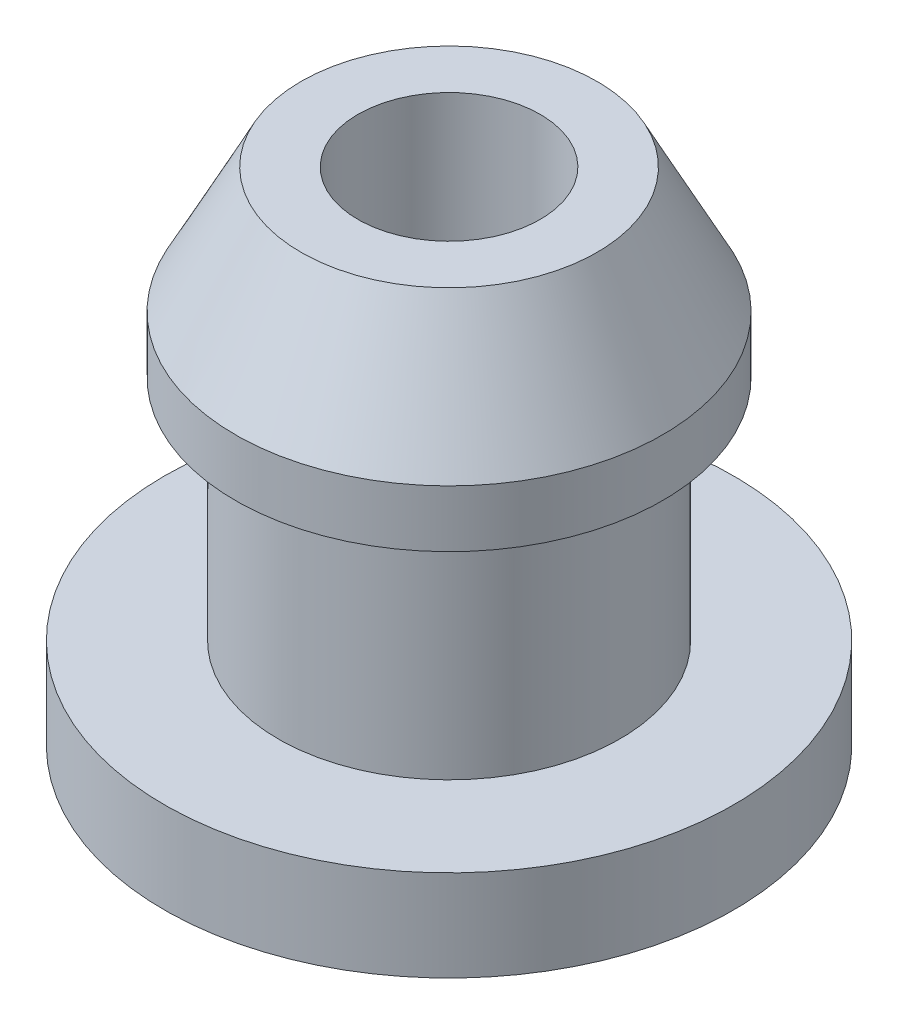
SolidWorks part; units mm, degrees
ref_plane "Plan de face" through (0, 0, 0) normal (0, 0, 1) x (1, 0, 0)
ref_plane "Plan de dessus" through (0, 0, 0) normal (0, 1, 0) x (1, 0, 0)
ref_plane "Plan de droite" through (0, 0, 0) normal (1, 0, 0) x (0, 0, -1)
sketch "Esquisse1" plane through (0, 0, 0) normal (0, 0, 1) x (1, 0, 0)
  line L0 (0, 5.28) -> (0, -4.4) construction
  line L1 (0, -4.4) -> (5, -4.4)
  line L2 (5, -4.4) -> (5, -2.8)
  line L3 (5, -2.8) -> (3, -2.8)
  line L4 (3, -2.8) -> (3, 1.2)
  line L5 (3, 1.2) -> (3.75, 1.2)
  line L6 (3.75, 1.2) -> (3.75, 2.2)
  line L7 (3.75, 2.2) -> (2.6, 4.4)
  line L8 (0, -1.6) -> (1.6, -1.6)
  line L9 (1.6, -1.6) -> (1.6, 4.4)
  line L10 (1.6, 4.4) -> (2.6, 4.4)
  line L11 (0, -1.6) -> (0, -4.4)
  dimension "D1" = 4
  dimension "D2" = 1.6
  dimension "D3" = 1.6
  dimension "D4" = 1
  dimension "D5" = 5
  dimension "D6" = 3
  dimension "D7" = 3.75
  dimension "D8" = 1
  dimension "D9" = 4.4
  dimension "D10" = 8.8
  dimension "D11" = 6
revolve "Révolution1" add sketch "Esquisse1" angle 360 about L0
